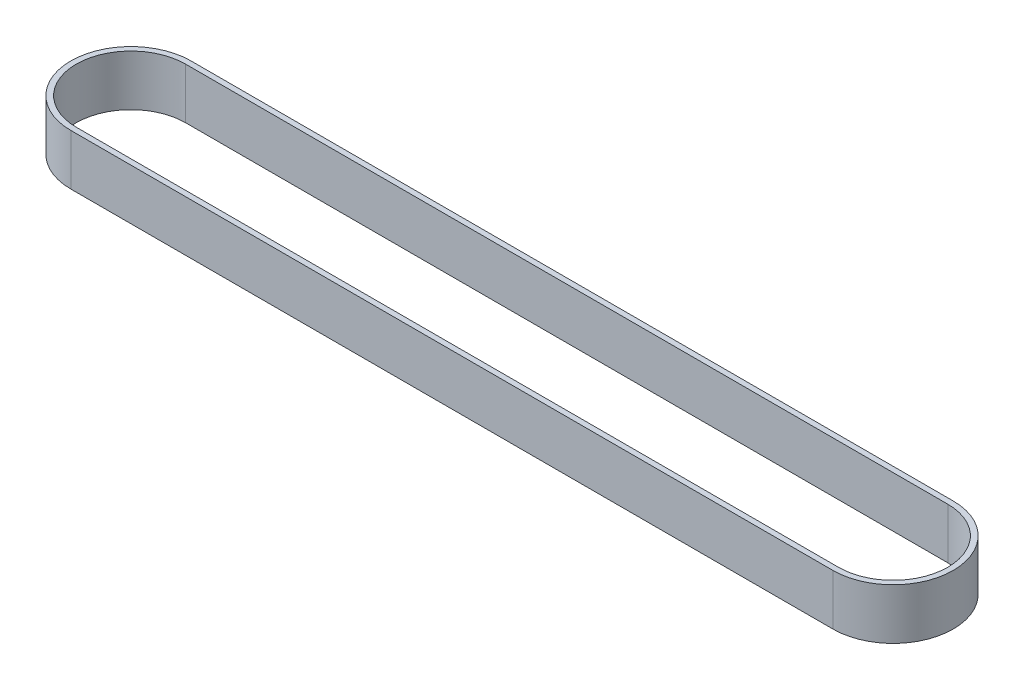
SolidWorks part; units mm, degrees
ref_plane "Front Plane" through (0, 0, 0) normal (0, 0, 1) x (1, 0, 0)
ref_plane "Top Plane" through (0, 0, 0) normal (0, 1, 0) x (1, 0, 0)
ref_plane "Right Plane" through (0, 0, 0) normal (1, 0, 0) x (0, 0, -1)
sketch "Sketch1" plane through (0, 0, 0) normal (0, 1, 0) x (1, 0, 0)
  line L0 (0, 0) -> (143, 0) construction
  line L1 (0, 11.285) -> (143, 11.285)
  line L2 (0, -11.285) -> (143, -11.285)
  line L3 (0, -11.285) -> (0, 11.285) construction
  line L4 (143, -11.285) -> (143, 11.285) construction
  arc A0 (143, -11.285) -> (143, 11.285) centre (143, 0) ccw
  arc A2 (0, 11.285) -> (0, -11.285) centre (0, 0) ccw
  point P7 (7.1723, 2.1928)
  point P8 (126, 0)
  point P9 (133.1723, 2.1928)
  point P14 (9.5, 0)
  point P16 (135.5, 0)
  dimension "D1" = 11.285
  dimension "D5" = 143
extrude "Boss-Extrude2" add sketch "Sketch1" along normal blind 9.53
sketch "Sketch2" plane through (0, 9.53, 0) normal (0, 1, 0) x (1, 0, 0)
  line L0 (0, 11.285) -> (143, 11.285) construction
  line L1 (0, -11.285) -> (143, -11.285) construction
  line L2 (0, 10.255) -> (143, 10.255)
  line L3 (0, -10.255) -> (143, -10.255)
  arc A1 (143, -11.285) -> (143, 11.285) centre (143, 0) ccw construction
  arc A2 (0, 11.285) -> (0, -11.285) centre (0, 0) ccw construction
  arc A3 (143, -10.255) -> (143, 10.255) centre (143, 0) ccw
  arc A4 (0, 10.255) -> (0, -10.255) centre (0, 0) ccw
  dimension "D1" = 1.03
extrude "Cut-Extrude1" cut sketch "Sketch2" against normal through all
